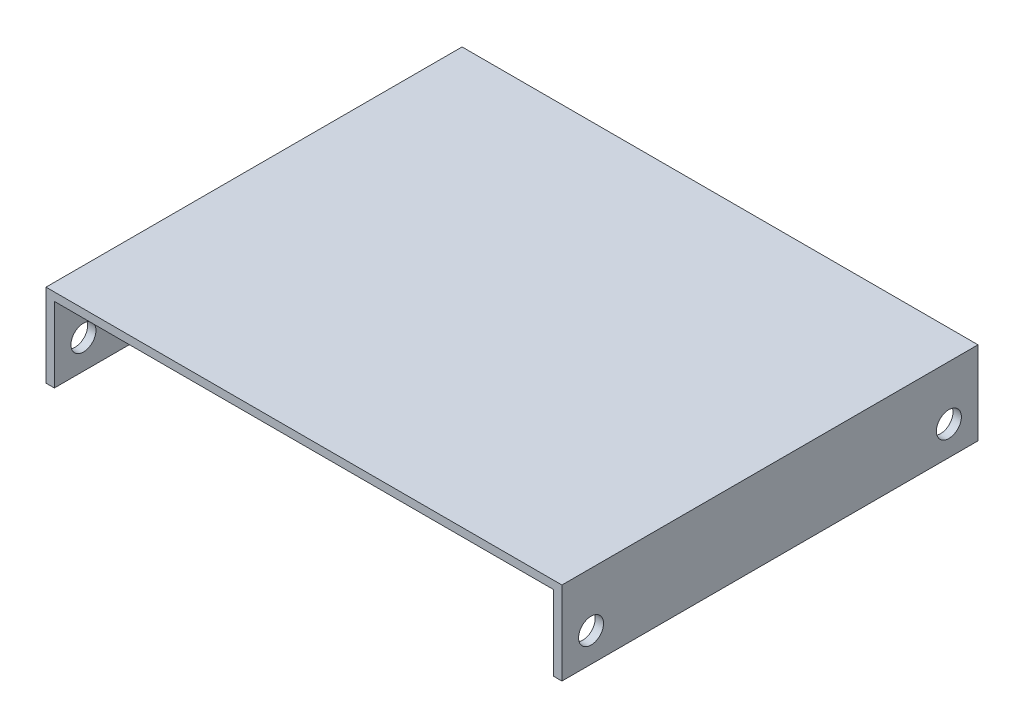
SolidWorks part; units mm, degrees
ref_plane "Front Plane" through (0, 0, 0) normal (0, 0, 1) x (1, 0, 0)
ref_plane "Top Plane" through (0, 0, 0) normal (0, 1, 0) x (1, 0, 0)
ref_plane "Right Plane" through (0, 0, 0) normal (1, 0, 0) x (0, 0, -1)
sketch "Sketch1" plane through (0, 0, 0) normal (0, 0, 1) x (1, 0, 0)
  line L0 (0, 0) -> (0, 20)
  line L1 (0, 20) -> (124, 20)
  line L2 (124, 20) -> (124, 0)
  line L3 (124, 0) -> (122, 0)
  line L4 (122, 0) -> (122, 18.0419)
  line L5 (2, 18.0419) -> (122, 18.0419)
  line L6 (0, 0) -> (2, 0)
  line L7 (2, 0) -> (2, 18.0419)
  dimension "D1" = 20
  dimension "D2" = 124
  dimension "D3" = 2
  dimension "D4" = 2
extrude "Boss-Extrude1" add sketch "Sketch1" along normal blind 100
sketch "Sketch2" plane through (124, 0, 0) normal (1, 0, 0) x (0, 0, -1)
  line L0 (-100, 0) -> (-93, 0) construction
  line L1 (-100, 0) -> (0, 0) construction
  line L2 (-93, 0) -> (-93, 7)
  circle A0 centre (-93, 7) radius 3
  dimension "D1" = 7
extrude "Cut-Extrude1" cut sketch "Sketch2" against normal blind 141 contours A0
sketch "Sketch3" plane through (124, 0, 0) normal (1, 0, 0) x (0, 0, -1)
  line L0 (0, 0) -> (-7, 0)
  line L1 (-100, 0) -> (0, 0) construction
  line L2 (-7, 0) -> (-7, 7)
  circle A0 centre (-7, 7) radius 3
  dimension "D1" = 7
extrude "Cut-Extrude2" cut sketch "Sketch3" against normal blind 141 contours A0
